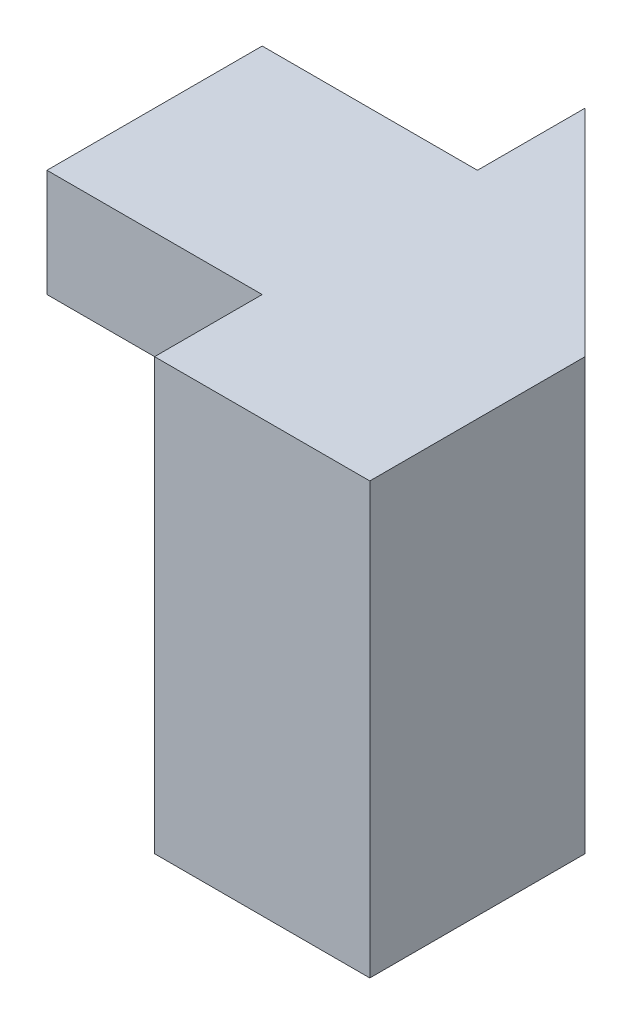
SolidWorks part; units mm, degrees
ref_plane "Front Plane" through (0, 0, 0) normal (0, 0, 1) x (1, 0, 0)
ref_plane "Top Plane" through (0, 0, 0) normal (0, 1, 0) x (1, 0, 0)
ref_plane "Right Plane" through (0, 0, 0) normal (1, 0, 0) x (0, 0, -1)
sketch "Sketch1" plane through (0, 0, 0) normal (0, 1, 0) x (1, 0, 0)
  line L0 (0, 0) -> (2, 0)
  line L1 (2, 0) -> (2, 2)
  line L2 (2, 2) -> (0, 4)
  line L3 (0, 4) -> (-2, 4)
  line L4 (-2, 4) -> (-2, 1)
  line L5 (-2, 1) -> (0, 1)
  line L6 (0, 1) -> (0, 0)
  dimension "D1" = 1
  dimension "D2" = 2
  dimension "D3" = 3
  dimension "D4" = 2
  dimension "D5" = 2
  dimension "D6" = 2
extrude "Boss-Extrude1" add sketch "Sketch1" along normal blind 4
sketch "Sketch2" plane through (-2, 0, 0) normal (-1, 0, 0) x (0, 0, 1)
  line L0 (-1, 3) -> (-2, 3)
  line L1 (-1, 4) -> (-1, 0) construction
  line L2 (-4, 0) -> (-1, 0) construction
  line L3 (-2, 0) -> (-1, 0)
  line L4 (-1, 0) -> (-1, 3)
  line L5 (-3, 4) -> (-3, 2)
  line L6 (-4, 4) -> (-1, 4) construction
  line L7 (-4, 4) -> (-4, 0) construction
  line L8 (-4, 2) -> (-4, 4)
  line L9 (-4, 4) -> (-3, 4)
  line L10 (-2, 3) -> (-2, 0)
  line L11 (-3, 2) -> (-4, 0)
  line L12 (-4, 0) -> (-4, 2)
  dimension "D1" = 3
  dimension "D2" = 1
  dimension "D3" = 1
  dimension "D4" = 2
  dimension "D5" = 2
extrude "Cut-Extrude1" cut sketch "Sketch2" against normal blind 2
